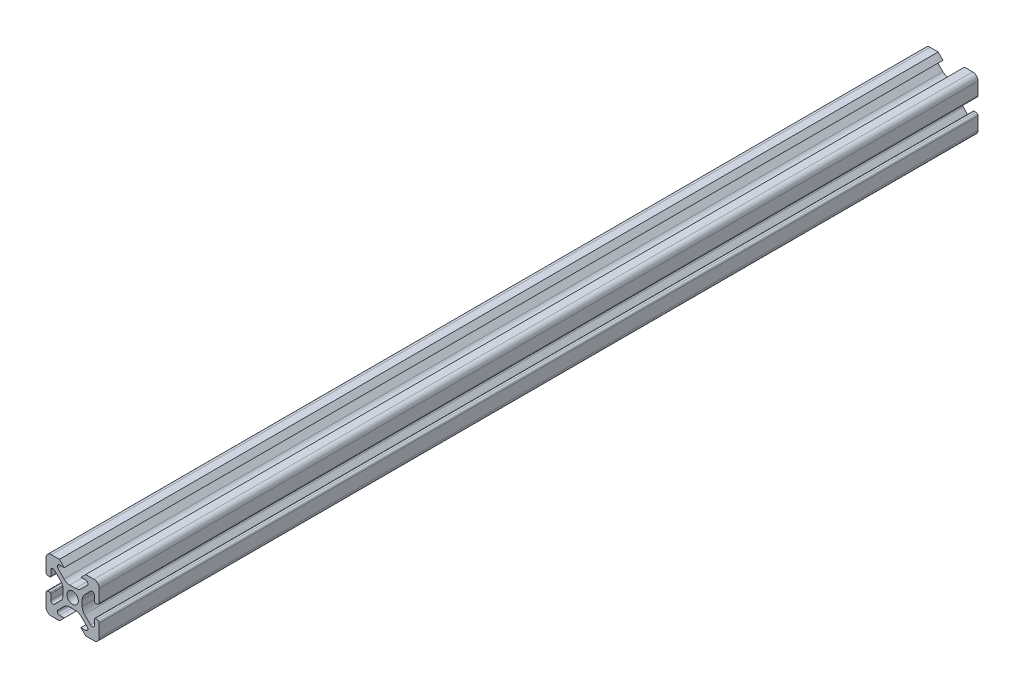
SolidWorks part; units mm, degrees
ref_plane "Front Plane" through (0, 0, 0) normal (0, 0, 1) x (1, 0, 0)
ref_plane "Top Plane" through (0, 0, 0) normal (0, 1, 0) x (1, 0, 0)
ref_plane "Right Plane" through (0, 0, 0) normal (1, 0, 0) x (0, 0, -1)
sketch "Sketch1" plane through (0, 0, 0) normal (0, 0, 1) x (1, 0, 0)
  line L0 (0, 10) -> (0, -10) construction
  line L1 (10, 0) -> (-10, 0) construction
  line L2 (-2.5, 10) -> (2.5, 10) construction
  line L3 (-5.75, 8.2) -> (5.75, 8.2) construction
  circle A0 centre (0, 0) radius 2.15 construction
  point P4 (0, 0)
  point P8 (0, 0)
  point P10 (0, 3.6)
  point P14 (0, 10)
  point P17 (0, 8.2)
  dimension "Thru Hole" = 4.3
  dimension "Height" = 20
  dimension "T Slot Depth" = 6.4
  dimension "T Slot Top Width" = 5
  dimension "T Slot Max Width" = 11.5
  dimension "Wall" = 1.8
sketch "Sketch2" plane through (0, 0, 0) normal (1, 0, 0) x (0, 0, -1)
  line L0 (152.4, 0) -> (-152.4, 0) construction
  point P4 (0, 0)
  dimension "D1" = 304.8
sketch "Sketch3" plane through (0, 0, 0) normal (0, 0, 1) x (1, 0, 0)
  line L0 (3.2874, 10) -> (8, 10)
  line L1 (10, 8) -> (10, -8) construction
  line L2 (8, -10) -> (-8, -10) construction
  line L3 (-10, 10) -> (10, -10) construction
  line L4 (2.5, 9.2126) -> (2.5, 8.5048)
  line L5 (-5.75, 8.2) -> (5.75, 8.2) construction
  line L6 (2.8048, 8.2) -> (4.9118, 8.2)
  line L7 (5.5045, 6.7691) -> (3.2141, 4.4787)
  line L8 (1.0928, 3.6) -> (-1.0928, 3.6)
  line L9 (0, 10) -> (0, -10) construction
  line L10 (5.75, 8.2) -> (5.75, 0) construction
  line L11 (10, 0) -> (-10, 0) construction
  line L12 (0, 0) -> (0, 10) construction
  line L13 (-2.5, 9.2126) -> (-2.5, 8.5048)
  line L14 (-5.5045, 6.7691) -> (-3.2141, 4.4787)
  line L15 (-2.8048, 8.2) -> (-4.9118, 8.2)
  line L16 (-3.2874, 10) -> (-8, 10)
  line L17 (0, 0) -> (-10, 0) construction
  line L18 (-10, 3.2874) -> (-10, 8)
  line L19 (-8.2, 2.8048) -> (-8.2, 4.9118)
  line L20 (-6.7691, 5.5045) -> (-4.4787, 3.2141)
  line L21 (-9.2126, 2.5) -> (-8.5048, 2.5)
  line L22 (-3.6, -1.0928) -> (-3.6, 1.0928)
  line L23 (-6.7691, -5.5045) -> (-4.4787, -3.2141)
  line L24 (-8.2, -2.8048) -> (-8.2, -4.9118)
  line L25 (-9.2126, -2.5) -> (-8.5048, -2.5)
  line L26 (-10, -3.2874) -> (-10, -8)
  line L27 (9.2126, -2.5) -> (8.5048, -2.5)
  line L28 (8.2, -2.8048) -> (8.2, -4.9118)
  line L29 (6.7691, -5.5045) -> (4.4787, -3.2141)
  line L30 (3.6, -1.0928) -> (3.6, 1.0928)
  line L31 (9.2126, 2.5) -> (8.5048, 2.5)
  line L32 (6.7691, 5.5045) -> (4.4787, 3.2141)
  line L33 (8.2, 2.8048) -> (8.2, 4.9118)
  line L34 (10, 8) -> (10, 3.2874)
  line L35 (10, -3.2874) -> (10, -8)
  line L36 (3.2874, -10) -> (8, -10)
  line L37 (-3.2874, -10) -> (-8, -10)
  line L38 (-6.7691, -5.5045) -> (-4.4787, -3.2141)
  line L39 (-2.8048, -8.2) -> (-4.9118, -8.2)
  line L40 (-5.5045, -6.7691) -> (-3.2141, -4.4787)
  line L41 (-2.5, -9.2126) -> (-2.5, -8.5048)
  line L42 (1.0928, -3.6) -> (-1.0928, -3.6)
  line L43 (5.5045, -6.7691) -> (3.2141, -4.4787)
  line L44 (2.8048, -8.2) -> (4.9118, -8.2)
  line L45 (2.5, -9.2126) -> (2.5, -8.5048)
  arc A0 (4.9118, 8.2) -> (5.5045, 6.7691) centre (4.9118, 7.3618) cw
  arc A1 (3.2141, 4.4787) -> (1.0928, 3.6) centre (1.0928, 6.6) cw
  circle A2 centre (0, 0) radius 2.15 construction
  circle A3 centre (0, 0) radius 2.15
  arc A4 (3.2874, 10) -> (2.5, 9.2126) centre (3.2874, 9.2126) ccw
  arc A5 (2.5, 8.5048) -> (2.8048, 8.2) centre (2.8048, 8.5048) ccw
  arc A6 (-3.2874, 10) -> (-2.5, 9.2126) centre (-3.2874, 9.2126) cw
  arc A7 (-4.9118, 8.2) -> (-5.5045, 6.7691) centre (-4.9118, 7.3618) ccw
  arc A8 (-3.2141, 4.4787) -> (-1.0928, 3.6) centre (-1.0928, 6.6) ccw
  arc A9 (-2.5, 8.5048) -> (-2.8048, 8.2) centre (-2.8048, 8.5048) cw
  arc A10 (-8.5048, 2.5) -> (-8.2, 2.8048) centre (-8.5048, 2.8048) ccw
  arc A11 (-4.4787, 3.2141) -> (-3.6, 1.0928) centre (-6.6, 1.0928) cw
  arc A12 (-8.2, 4.9118) -> (-6.7691, 5.5045) centre (-7.3618, 4.9118) cw
  arc A13 (-10, 3.2874) -> (-9.2126, 2.5) centre (-9.2126, 3.2874) ccw
  arc A14 (-8.5048, -2.5) -> (-8.2, -2.8048) centre (-8.5048, -2.8048) cw
  arc A15 (-10, -3.2874) -> (-9.2126, -2.5) centre (-9.2126, -3.2874) cw
  arc A16 (-4.4787, -3.2141) -> (-3.6, -1.0928) centre (-6.6, -1.0928) ccw
  arc A17 (-8.2, -4.9118) -> (-6.7691, -5.5045) centre (-7.3618, -4.9118) ccw
  arc A26 (-8, -10) -> (-10, -8) centre (-8, -8) cw
  arc A27 (-8, 10) -> (-10, 8) centre (-8, 8) ccw
  arc A28 (8, 10) -> (10, 8) centre (8, 8) cw
  arc A29 (10, -8) -> (8, -10) centre (8, -8) cw
  arc A30 (8.2, -4.9118) -> (6.7691, -5.5045) centre (7.3618, -4.9118) cw
  arc A31 (4.4787, -3.2141) -> (3.6, -1.0928) centre (6.6, -1.0928) cw
  arc A32 (10, -3.2874) -> (9.2126, -2.5) centre (9.2126, -3.2874) ccw
  arc A33 (8.5048, -2.5) -> (8.2, -2.8048) centre (8.5048, -2.8048) ccw
  arc A34 (10, 3.2874) -> (9.2126, 2.5) centre (9.2126, 3.2874) cw
  arc A35 (8.2, 4.9118) -> (6.7691, 5.5045) centre (7.3618, 4.9118) ccw
  arc A36 (4.4787, 3.2141) -> (3.6, 1.0928) centre (6.6, 1.0928) ccw
  arc A37 (8.5048, 2.5) -> (8.2, 2.8048) centre (8.5048, 2.8048) cw
  arc A38 (-2.5, -8.5048) -> (-2.8048, -8.2) centre (-2.8048, -8.5048) ccw
  arc A39 (-3.2141, -4.4787) -> (-1.0928, -3.6) centre (-1.0928, -6.6) cw
  arc A40 (-4.9118, -8.2) -> (-5.5045, -6.7691) centre (-4.9118, -7.3618) cw
  arc A41 (-3.2874, -10) -> (-2.5, -9.2126) centre (-3.2874, -9.2126) ccw
  arc A42 (2.5, -8.5048) -> (2.8048, -8.2) centre (2.8048, -8.5048) cw
  arc A43 (3.2874, -10) -> (2.5, -9.2126) centre (3.2874, -9.2126) cw
  arc A44 (3.2141, -4.4787) -> (1.0928, -3.6) centre (1.0928, -6.6) ccw
  arc A45 (4.9118, -8.2) -> (5.5045, -6.7691) centre (4.9118, -7.3618) ccw
  point P36 (2.5, 10)
  point P39 (2.5, 8.2)
  point P49 (0, 3.6)
  point P77 (-3.6, 0)
  point P78 (-8.2, -2.5)
  point P79 (-10, -2.5)
  point P104 (-10, -10)
  point P110 (10, 10)
  point P114 (10, -2.5)
  point P115 (8.2, -2.5)
  point P116 (3.6, 0)
  point P141 (0, -3.6)
  dimension "D1" = 3
  dimension "D2" = 0.8382
  dimension "D4" = 0.7874
  dimension "D5" = 0.3048
  dimension "D6" = 2
  dimension "D3" = 45
extrude "Boss-Extrude1" add sketch "Sketch3" along normal blind 330.2 contours A45 L44 A42 L45 A43 L36 A29 L35 A32 L27 A33 L28 A30 L29 A31 L30 A36 L32 A35 L33 A37 L31 A34 L34 A28 L0 A4 L4 A5 L6 A0 L7 A1 L8 A8 L14 A7 L15 A9 L13 A6 L16 A27 L18 A13 L21 A10 L19 A12 L20 A11
sketch "Sketch4" plane through (0, 0, 330.2) normal (0, 0, 1) x (1, 0, 0)
  line L0 (-6.0187, 11.0657) -> (-2.0187, 7.0657)
  line L1 (1.9813, 7.0657) -> (5.9813, 11.0657)
  line L2 (5.9813, 11.0657) -> (-6.0187, 11.0657)
  line L3 (-2.0187, 7.0657) -> (1.9813, 7.0657)
  line L4 (-0.0187, 0) -> (-0.0187, -14.091) construction
  line L5 (0, 0) -> (25.4832, 0) construction
  line L6 (1.9813, -7.0657) -> (5.9813, -11.0657)
  line L7 (-2.0187, -7.0657) -> (1.9813, -7.0657)
  line L8 (5.9813, -11.0657) -> (-6.0187, -11.0657)
  line L9 (-6.0187, -11.0657) -> (-2.0187, -7.0657)
  point P14 (0, 0)
  dimension "D1" = 45
  dimension "D2" = 45
  dimension "D3" = 90
  dimension "D4" = 4
  dimension "D5" = 2
  dimension "D6" = 12
extrude "Cut-Extrude1" cut sketch "Sketch4" against normal through all
